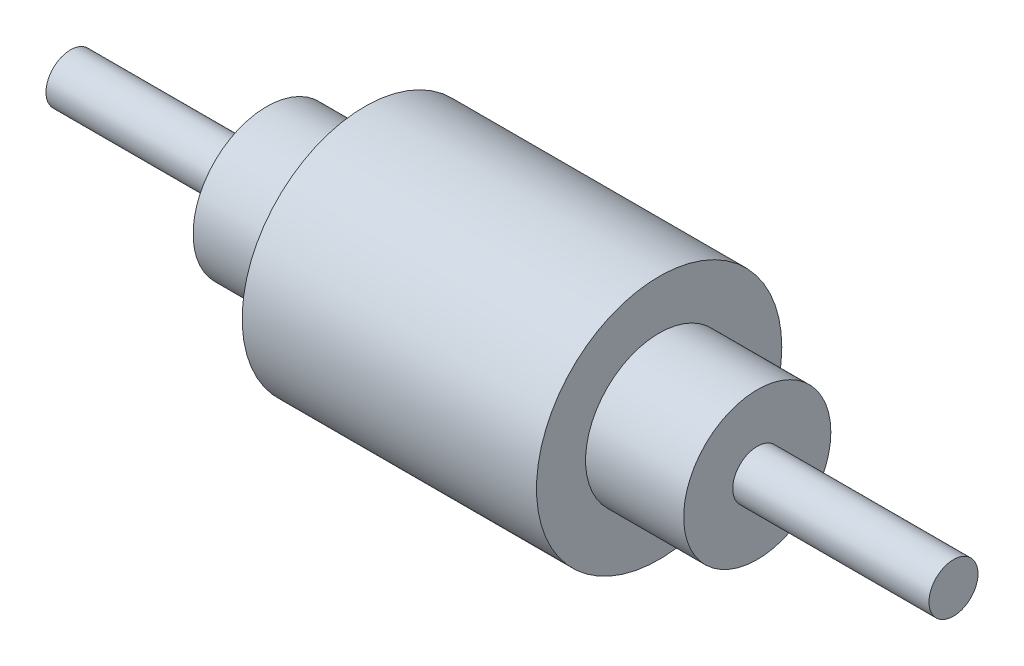
SolidWorks part; units mm, degrees
ref_plane "Front Plane" through (0, 0, 0) normal (0, 0, 1) x (1, 0, 0)
ref_plane "Top Plane" through (0, 0, 0) normal (0, 1, 0) x (1, 0, 0)
ref_plane "Right Plane" through (0, 0, 0) normal (1, 0, 0) x (0, 0, -1)
sketch "Sketch1" plane through (0, 0, 0) normal (0, 0, 1) x (1, 0, 0)
  line L8 (180, 0) -> (-180, 0)
  line L9 (-180, 0) -> (-180, 10)
  line L10 (-180, 10) -> (-100, 10)
  line L11 (-100, 10) -> (-100, 30)
  line L12 (-100, 30) -> (-60, 30)
  line L13 (-60, 30) -> (-60, 50)
  line L14 (-60, 50) -> (60, 50)
  line L15 (0, 50) -> (0, 0)
  line L16 (180, 0) -> (180, 10)
  line L17 (180, 10) -> (100, 10)
  line L18 (100, 10) -> (100, 30)
  line L19 (60, 30) -> (60, 50)
  line L20 (100, 30) -> (60, 30)
  dimension "D1" = 180
  dimension "D2" = 120
  dimension "D3" = 80
  dimension "D4" = 10
  dimension "D5" = 30
  dimension "D6" = 50
revolve "Revolve1" add sketch "Sketch1" angle 360 about L8
